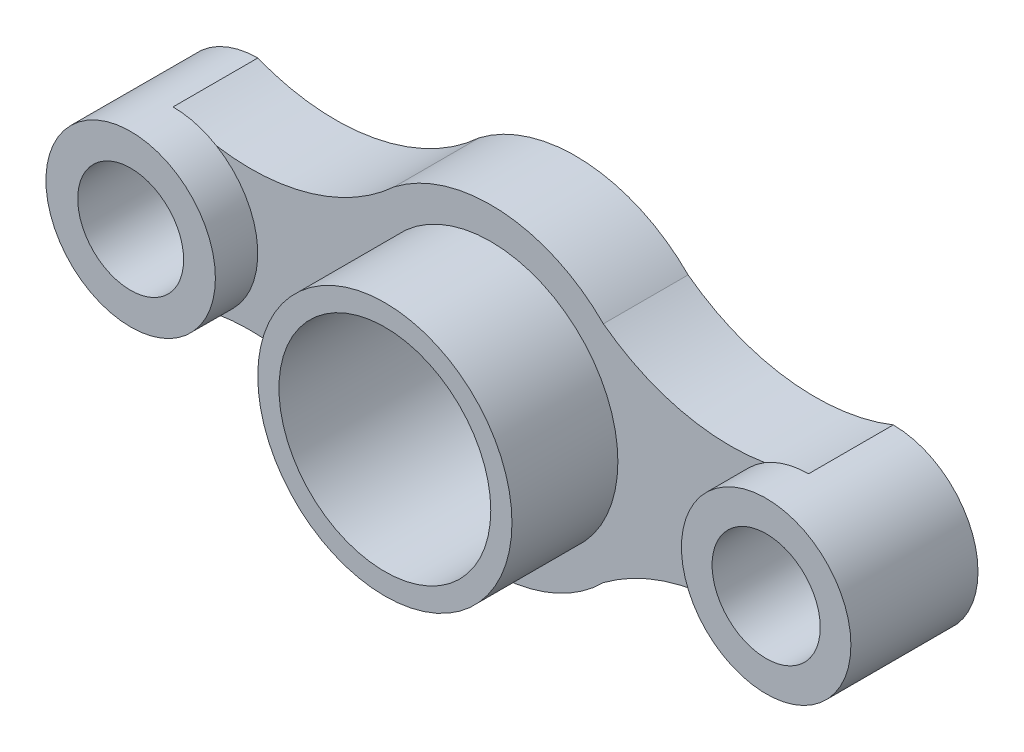
SolidWorks part; units mm, degrees
ref_plane "Front Plane" through (0, 0, 0) normal (0, 0, 1) x (1, 0, 0)
ref_plane "Top Plane" through (0, 0, 0) normal (0, 1, 0) x (1, 0, 0)
ref_plane "Right Plane" through (0, 0, 0) normal (1, 0, 0) x (0, 0, -1)
sketch "Sketch1" plane through (0, 0, 0) normal (0, 0, 1) x (1, 0, 0)
  line L0 (-150, 0) -> (150, 0)
  line L1 (0, 109.4955) -> (0, -109.4955)
  line L2 (0, 75) -> (0, 95.0213) construction
  circle A0 centre (0, 0) radius 75
  circle A1 centre (-150, 0) radius 25
  circle A2 centre (-150, 0) radius 40
  arc A3 (-150, 40) -> (-45.4654, 59.6481) centre (-113.3761, 133.0521) ccw
  arc A4 (-45.4654, 59.6481) -> (53.1614, 52.9043) centre (0, 0) cw
  circle A5 centre (150, 0) radius 25.5318
  circle A6 centre (150, 0) radius 25
  circle A7 centre (150, 0) radius 40
  arc A8 (53.1614, 52.9043) -> (150, 40) centre (113.1064, 132.9455) ccw
  arc A9 (-150, -40) -> (-45.4654, -59.6481) centre (-113.3761, -133.0521) cw
  arc A10 (53.1614, -52.9043) -> (150, -40) centre (113.1064, -132.9455) cw
  arc A11 (-150, 40) -> (-150, -40) centre (-150, 0) ccw
  arc A12 (150, 40) -> (150, -40) centre (150, 0) cw
  arc A13 (-45.4654, -59.6481) -> (53.1614, -52.9043) centre (0, 0) ccw
  point P4 (0, 0)
  point P8 (0, 0)
  dimension "D2" = 150
  dimension "D3" = 50
  dimension "D4" = 80
  dimension "D5" = 100
  dimension "D6" = 50
  dimension "D7" = 80
  dimension "D8" = 100
  dimension "D1" = 300
extrude "Boss-Extrude1" add sketch "Sketch1" along normal blind 40
sketch "Sketch2" plane through (0, 0, 40) normal (0, 0, 1) x (1, 0, 0)
  circle A0 centre (-150, 0) radius 40
  circle A1 centre (-150, 0) radius 25
  circle A2 centre (150, 0) radius 25.5318
  circle A3 centre (150, 0) radius 40
  dimension "D1" = 80
  dimension "D2" = 50
extrude "Boss-Extrude2" add sketch "Sketch2" along normal blind 20
sketch "Sketch3" plane through (0, 0, 40) normal (0, 0, 1) x (1, 0, 0)
  circle A0 centre (0, 0) radius 60
  circle A1 centre (0, 0) radius 50
  dimension "D1" = 100
  dimension "D2" = 120
extrude "Boss-Extrude3" add sketch "Sketch3" along normal blind 50
sketch "Sketch4" plane through (0, 0, 40) normal (0, 0, 1) x (1, 0, 0)
  circle A0 centre (0, 0) radius 50
extrude "Cut-Extrude1" cut sketch "Sketch4" against normal blind 50
